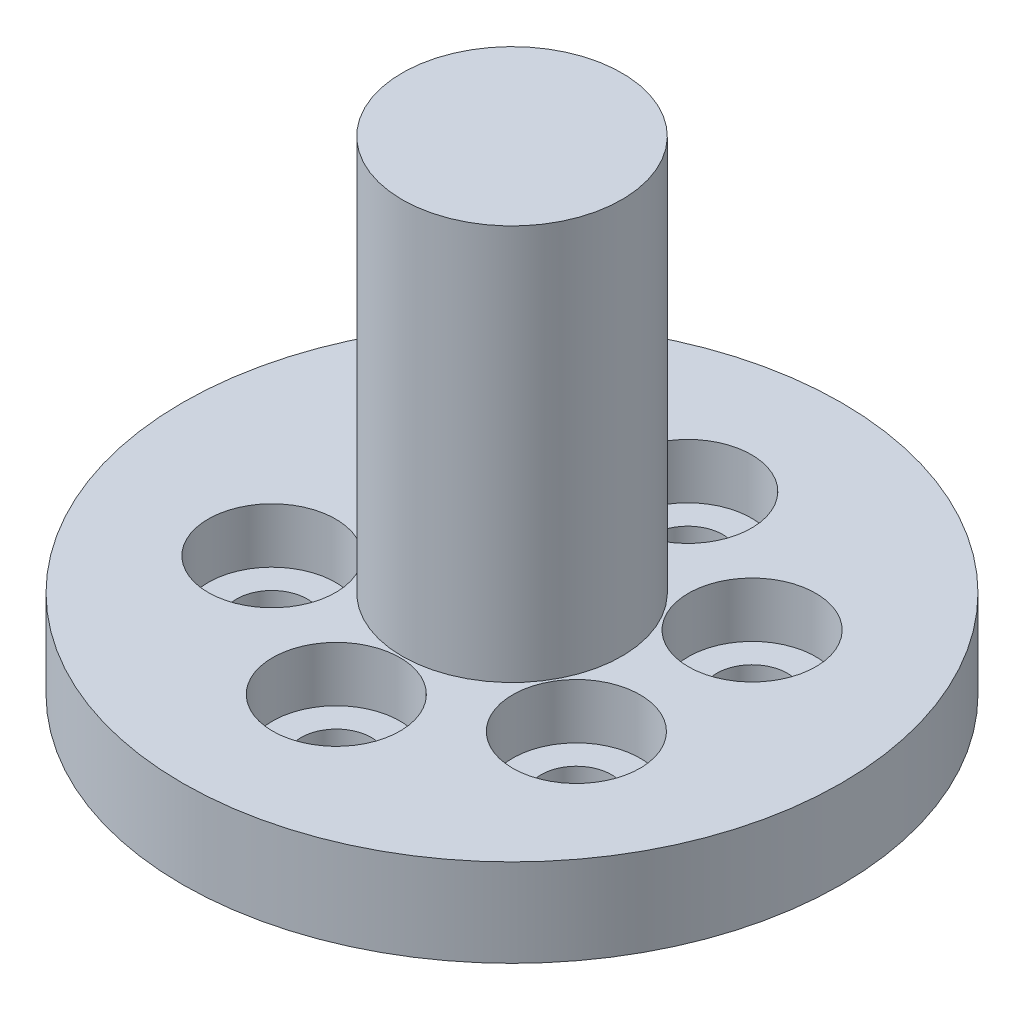
SolidWorks part; units mm, degrees
ref_plane "前视基准面" through (0, 0, 0) normal (0, 0, 1) x (1, 0, 0)
ref_plane "上视基准面" through (0, 0, 0) normal (0, 1, 0) x (1, 0, 0)
ref_plane "右视基准面" through (0, 0, 0) normal (1, 0, 0) x (0, 0, -1)
sketch "草图1" plane through (0, 0, 0) normal (0, 1, 0) x (1, 0, 0)
  circle A0 centre (0, 0) radius 15
  dimension "D1" = 30
extrude "凸台-拉伸1" add sketch "草图1" along normal blind 4
sketch "草图2" plane through (0, 4, 0) normal (0, 1, 0) x (1, 0, 0)
  circle A0 centre (0, 0) radius 8 construction
  circle A1 centre (0, 8) radius 1.6
  circle A2 centre (6.9282, 4) radius 1.6
  circle A3 centre (6.9282, -4) radius 1.6
  circle A4 centre (0, -8) radius 1.6
  circle A5 centre (-6.9282, -4) radius 1.6
  circle A6 centre (-6.9282, 4) radius 1.6
  point P18 (0, 0)
  dimension "D1" = 16
  dimension "D2" = 3.2
  dimension "D3" = 6
extrude "切除-拉伸1" cut sketch "草图2" against normal blind 5
sketch "草图3" plane through (0, 4, 0) normal (0, 1, 0) x (1, 0, 0)
  circle A0 centre (0, 0) radius 8 construction
  circle A1 centre (0, 8) radius 2.9
  circle A2 centre (0.0005, 0.0009) radius 8 construction
  circle A3 centre (6.9287, 4.0009) radius 2.9
  circle A4 centre (0.0015, 0.0009) radius 8 construction
  circle A5 centre (6.9297, -3.9991) radius 2.9
  circle A6 centre (0.002, 0) radius 8 construction
  circle A7 centre (0.002, -8) radius 2.9
  circle A8 centre (0.0015, -0.0009) radius 8 construction
  circle A9 centre (-6.9267, -4.0009) radius 2.9
  circle A10 centre (0.0005, -0.0009) radius 8 construction
  circle A11 centre (-6.9277, 3.9991) radius 2.9
  point P27 (0.001, 0)
  dimension "D1" = 16
  dimension "D2" = 5.8
  dimension "D3" = 6
extrude "切除-拉伸2" cut sketch "草图3" against normal blind 2.5
sketch "草图4" plane through (0, 4, 0) normal (0, 1, 0) x (1, 0, 0)
  circle A0 centre (0, 0) radius 5
  dimension "D1" = 10
extrude "凸台-拉伸2" add sketch "草图4" along normal blind 18
sketch "草图5" plane through (0, 0, 0) normal (0, -1, 0) x (1, 0, 0)
  circle A0 centre (0, 0) radius 4
  dimension "D1" = 8
extrude "切除-拉伸3" cut sketch "草图5" against normal blind 2
